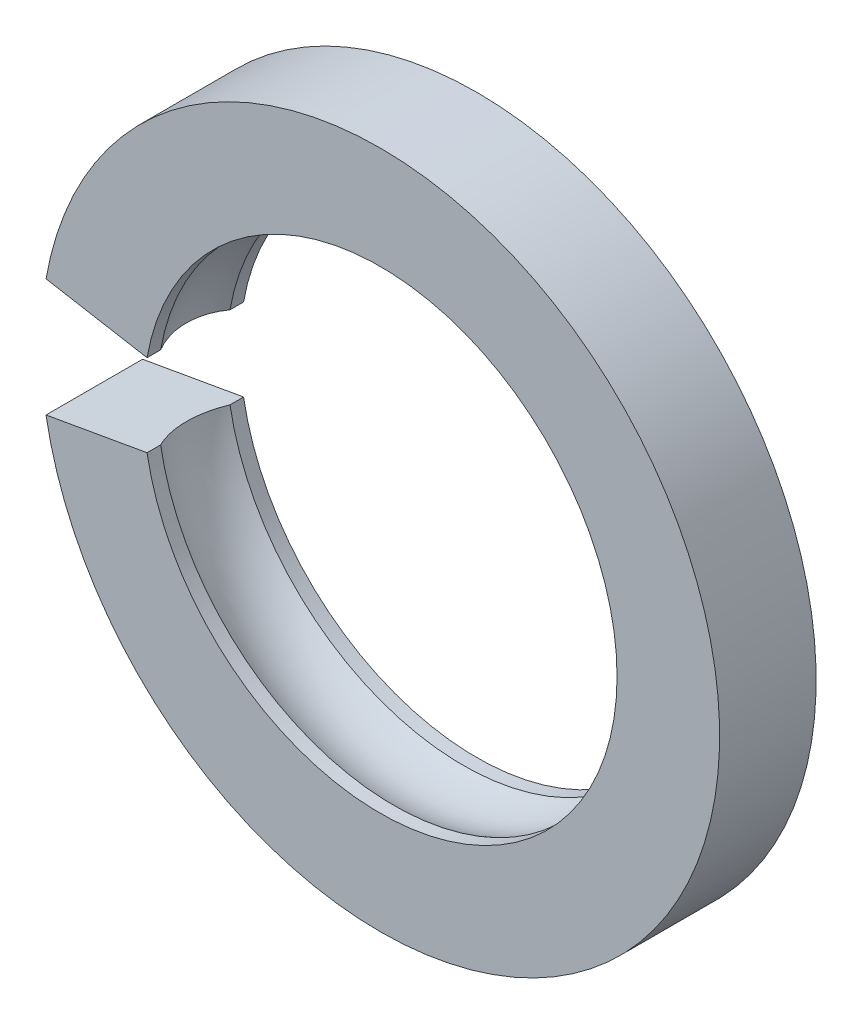
SolidWorks part; units mm, degrees
ref_plane "Front Plane" through (0, 0, 0) normal (0, 0, 1) x (1, 0, 0)
ref_plane "Top Plane" through (0, 0, 0) normal (0, 1, 0) x (1, 0, 0)
ref_plane "Right Plane" through (0, 0, 0) normal (1, 0, 0) x (0, 0, -1)
sketch "Sketch1" plane through (0, 0, 0) normal (0, 0, 1) x (1, 0, 0)
  circle A0 centre (0, 0) radius 15.7
  circle A1 centre (0, 0) radius 22.5
  dimension "D1" = 31.4
  dimension "D2" = 45
extrude "Boss-Extrude1" add sketch "Sketch1" along normal blind 6.4
sketch "Sketch2" plane through (0, 0, 0) normal (0, 0, 1) x (1, 0, 0)
  line L0 (0, -1000) -> (0, 49000) construction
  line L1 (-984.8078, 173.6482) -> (48255.5799, -8508.7607) construction
  line L2 (-984.8078, -173.6482) -> (48255.5799, 8508.7607) construction
  line L3 (0, 0) -> (-29.6455, 5.2273)
  line L4 (0, 0) -> (-29.6455, -5.2273)
  line L5 (-29.6455, -5.2273) -> (-29.6455, 5.2273)
extrude "Cut-Extrude1" cut sketch "Sketch2" along normal through all
ref_plane "Plane1" through (0, 0, 0) normal (-0.1736, -0.9848, 0) x (-0.9848, 0.1736, 0)
sketch "Sketch5" plane through (0, 0, 0) normal (-0.1736, -0.9848, 0) x (-0.9848, 0.1736, 0)
  line L0 (15.7, -5.5) -> (16.4, -5.5) construction
  line L1 (15.7, -6.4) -> (15.7, 0) construction
  line L2 (15.7, -6.4) -> (22.5, -6.4) construction
  line L3 (15.7, -0.9) -> (17.4523, -0.9) construction
  line L4 (15.7, -0.9) -> (15.7, -5.5)
  line L5 (15.7, -3.2) -> (16.3, -3.2) construction
  arc A0 (15.7, -0.9) -> (15.7, -5.5) centre (11.6014, -3.2) cw
  dimension "D1" = 0.6
  dimension "D2" = 0.9
  dimension "D3" = 4.6
ref_axis "Axis1" through (0, 0, -0.32) along (0, 0, 1)
revolve "Cut-Revolve1" cut sketch "Sketch5" angle 360 about axis through (0, 0, -0.32) along (0, 0, 1)
